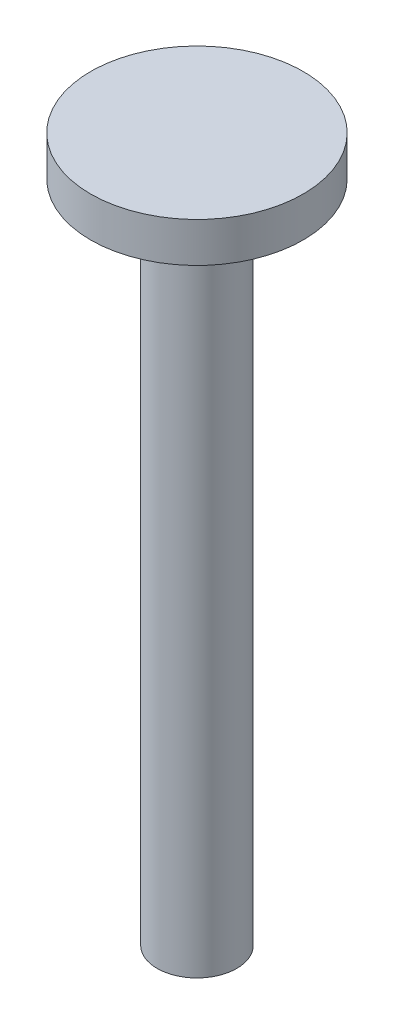
SolidWorks part; units mm, degrees
ref_plane "Front Plane" through (0, 0, 0) normal (0, 0, 1) x (1, 0, 0)
ref_plane "Top Plane" through (0, 0, 0) normal (0, 1, 0) x (1, 0, 0)
ref_plane "Right Plane" through (0, 0, 0) normal (1, 0, 0) x (0, 0, -1)
sketch "Sketch1" plane through (0, 0, 0) normal (0, 1, 0) x (1, 0, 0)
  circle A1 centre (0, 0) radius 4
  dimension "D1" = 8
extrude "Boss-Extrude1" add sketch "Sketch1" along normal blind 1.5
sketch "Sketch5" plane through (0, 0, 0) normal (0, -1, 0) x (-1, 0, 0)
  circle A1 centre (0, 0) radius 1.5
  dimension "D2" = 3
extrude "Boss-Extrude3" add sketch "Sketch5" along normal blind 25
